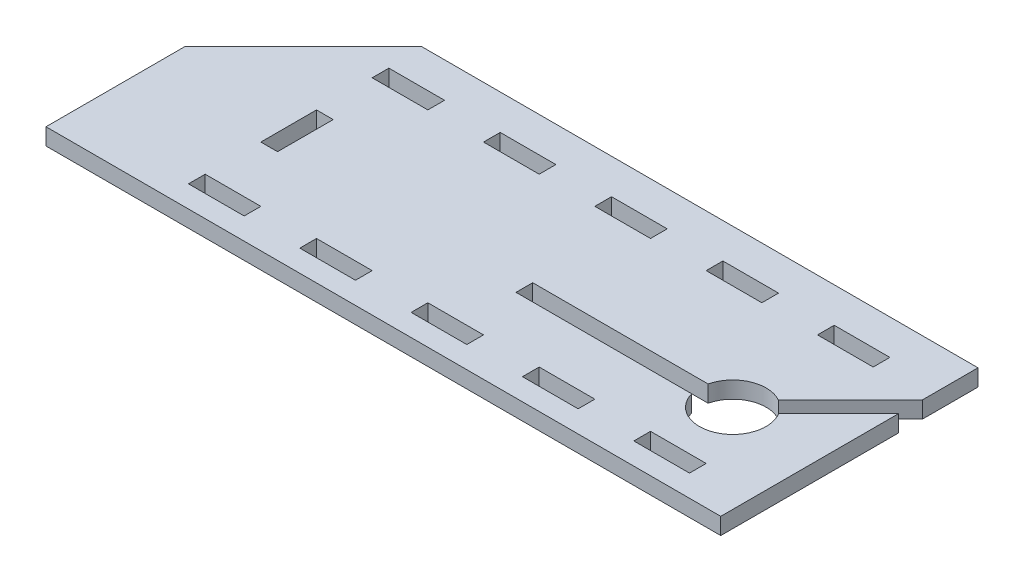
SolidWorks part; units mm, degrees
ref_plane "Plan de face" through (0, 0, 0) normal (0, 0, 1) x (1, 0, 0)
ref_plane "Plan de dessus" through (0, 0, 0) normal (0, 1, 0) x (1, 0, 0)
ref_plane "Plan de droite" through (0, 0, 0) normal (1, 0, 0) x (0, 0, -1)
sketch "Esquisse1" plane through (0, 0, 0) normal (0, 1, 0) x (1, 0, 0)
  line L0 (56.0682, -44.0125) -> (57.3933, -47.4605) construction
  line L1 (-48.5864, -63.7908) -> (72.6268, -63.7908)
  line L2 (-48.5864, -63.7908) -> (-48.5864, -38.7908)
  line L3 (-27.3732, -17.5776) -> (72.6268, -17.5776)
  line L4 (72.6268, -63.7908) -> (72.6268, -31.8203)
  line L5 (19.3935, -44.3365) -> (50.8963, -44.3365)
  line L6 (19.3935, -44.3365) -> (19.3935, -47.3365)
  line L7 (19.3935, -47.3365) -> (50.948, -47.3365)
  line L9 (59.6884, -40.5161) -> (72.6268, -27.5776)
  line L11 (61.8462, -42.6009) -> (72.6268, -31.8203)
  line L13 (-27.3732, -17.5776) -> (-48.5864, -38.7908)
  line L14 (72.6268, -27.5776) -> (72.6268, -17.5776)
  line L15 (-6.9072, -23.8748) -> (-6.9072, -26.8748)
  line L16 (-26.9072, -23.8748) -> (-16.9072, -23.8748)
  line L17 (-26.9072, -23.8748) -> (-26.9072, -26.8748)
  line L18 (-26.9072, -26.8748) -> (-16.9072, -26.8748)
  line L19 (-16.9072, -23.8748) -> (-16.9072, -26.8748)
  line L20 (-6.9072, -23.8748) -> (3.0928, -23.8748)
  line L21 (3.0928, -23.8748) -> (3.0928, -26.8748)
  line L22 (-6.9072, -26.8748) -> (3.0928, -26.8748)
  line L23 (13.0928, -23.8748) -> (13.0928, -26.8748)
  line L24 (13.0928, -23.8748) -> (23.0928, -23.8748)
  line L25 (23.0928, -23.8748) -> (23.0928, -26.8748)
  line L26 (13.0928, -26.8748) -> (23.0928, -26.8748)
  line L27 (33.0928, -23.8748) -> (33.0928, -26.8748)
  line L28 (33.0928, -23.8748) -> (43.0928, -23.8748)
  line L29 (43.0928, -23.8748) -> (43.0928, -26.8748)
  line L30 (33.0928, -26.8748) -> (43.0928, -26.8748)
  line L31 (53.0928, -23.8748) -> (53.0928, -26.8748)
  line L32 (53.0928, -23.8748) -> (63.0928, -23.8748)
  line L33 (63.0928, -23.8748) -> (63.0928, -26.8748)
  line L34 (53.0928, -26.8748) -> (63.0928, -26.8748)
  line L35 (-26.9072, -56.8748) -> (-16.9072, -56.8748)
  line L36 (-26.9072, -56.8748) -> (-26.9072, -59.8748)
  line L37 (-26.9072, -59.8748) -> (-16.9072, -59.8748)
  line L38 (-16.9072, -56.8748) -> (-16.9072, -59.8748)
  line L39 (-6.9072, -56.8748) -> (3.0928, -56.8748)
  line L40 (-6.9072, -56.8748) -> (-6.9072, -59.8748)
  line L41 (-6.9072, -59.8748) -> (3.0928, -59.8748)
  line L42 (3.0928, -56.8748) -> (3.0928, -59.8748)
  line L43 (13.0928, -56.8748) -> (23.0928, -56.8748)
  line L44 (13.0928, -56.8748) -> (13.0928, -59.8748)
  line L45 (13.0928, -59.8748) -> (23.0928, -59.8748)
  line L46 (23.0928, -56.8748) -> (23.0928, -59.8748)
  line L47 (33.0928, -56.8748) -> (43.0928, -56.8748)
  line L48 (33.0928, -56.8748) -> (33.0928, -59.8748)
  line L49 (33.0928, -59.8748) -> (43.0928, -59.8748)
  line L50 (43.0928, -56.8748) -> (43.0928, -59.8748)
  line L51 (53.0928, -56.8748) -> (63.0928, -56.8748)
  line L52 (53.0928, -56.8748) -> (53.0928, -59.8748)
  line L53 (53.0928, -59.8748) -> (63.0928, -59.8748)
  line L54 (63.0928, -56.8748) -> (63.0928, -59.8748)
  line L55 (-26.9072, -26.8748) -> (-26.9072, -36.8748) construction
  line L56 (-26.9072, -36.8748) -> (-23.9072, -36.8748)
  line L57 (-26.9072, -36.8748) -> (-26.9072, -46.8748)
  line L58 (-26.9072, -46.8748) -> (-23.9072, -46.8748)
  line L59 (-23.9072, -36.8748) -> (-23.9072, -46.8748)
  line L60 (-26.9072, -46.8748) -> (-26.9072, -56.8748) construction
  arc A0 (59.6884, -40.5161) -> (50.8963, -44.3365) centre (56.7307, -45.7365) ccw
  arc A1 (50.948, -47.3365) -> (61.8462, -42.6009) centre (56.7307, -45.7365) ccw
  dimension "D8" = 12
  dimension "D1" = 3
  dimension "D2" = 3
  dimension "D3" = 135
  dimension "D4" = 135
  dimension "D5" = 38
  dimension "D6" = 100
  dimension "D7" = 25
  dimension "D9" = 30
  dimension "D10" = 10
  dimension "D11" = 10
  dimension "D12" = 3
  dimension "D15" = 3
  dimension "D16" = 10
  dimension "D17" = 10
  dimension "D18" = 3
  dimension "D19" = 10
  dimension "D13" = 5
  dimension "D14" = 5
extrude "Boss.-Extru.1" add sketch "Esquisse1" along normal blind 3
